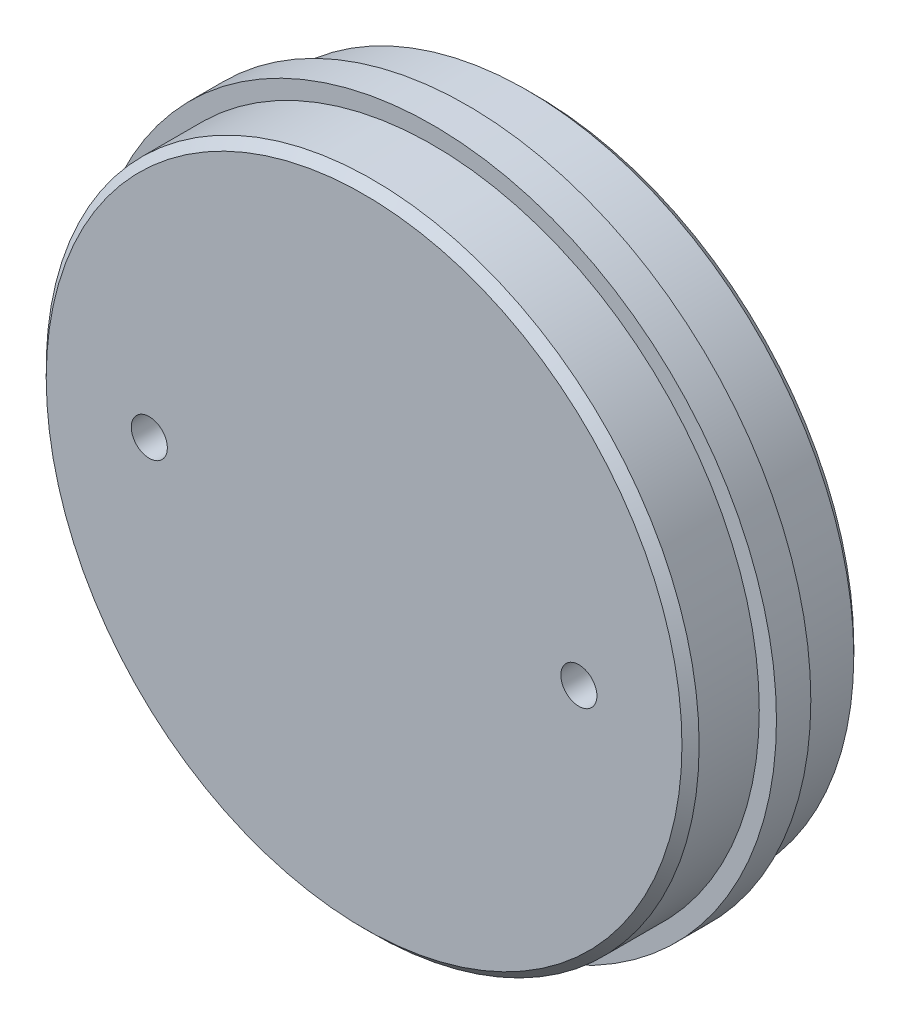
SolidWorks part; units mm, degrees
material "PPE"
ref_plane "Plan de face" through (0, 0, 0) normal (0, 0, 1) x (1, 0, 0)
ref_plane "Plan de dessus" through (0, 0, 0) normal (0, 1, 0) x (1, 0, 0)
ref_plane "Plan de droite" through (0, 0, 0) normal (1, 0, 0) x (0, 0, -1)
sketch "Esquisse1" plane through (0, 0, 0) normal (0, 0, 1) x (1, 0, 0)
  circle A0 centre (0, 0) radius 40
extrude "Boss.-Extru.1" add sketch "Esquisse1" along normal blind 4
sketch "Esquisse2" plane through (0, 0, 4) normal (0, 0, 1) x (1, 0, 0)
  circle A0 centre (0, 0) radius 38
extrude "Boss.-Extru.2" add sketch "Esquisse2" along normal blind 8 and the other way blind 12
chamfer "Chanfrein1" distance 1 angle 45 2 edges at (38, 0, 12) (38, 0, -8)
sketch "Esquisse3" plane through (0, 0, 12) normal (0, 0, 1) x (1, 0, 0)
  circle A0 centre (25, 0) radius 2.1
  circle A1 centre (-25, 0) radius 2.1
extrude "Enlèv. mat.-Extru.1" cut sketch "Esquisse3" against normal through all
